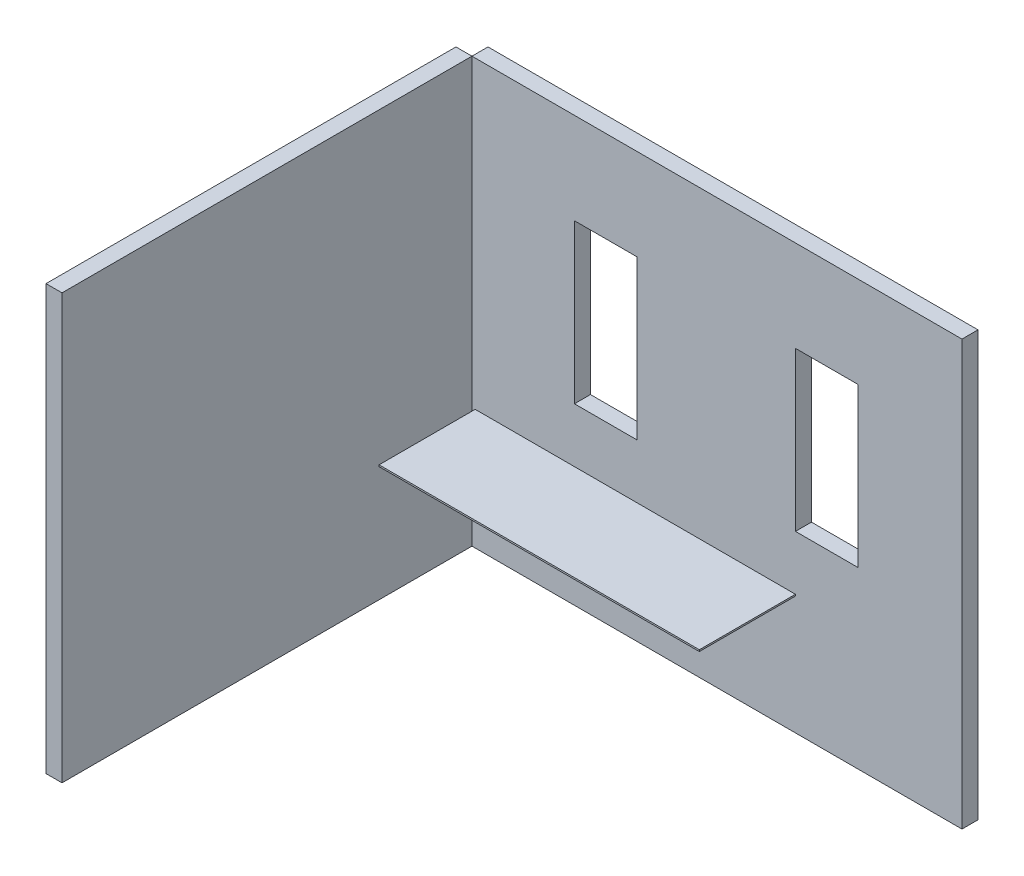
SolidWorks part; units mm, degrees
ref_plane "Plano frontal" through (0, 0, 0) normal (0, 0, 1) x (1, 0, 0)
ref_plane "Plano superior" through (0, 0, 0) normal (0, 1, 0) x (1, 0, 0)
ref_plane "Plano direito" through (0, 0, 0) normal (1, 0, 0) x (0, 0, -1)
sketch "Esboço6" plane through (0, 0, 0) normal (0, 0, 1) x (1, 0, 0)
  line L1 (0, 0) -> (3060, 0)
  line L2 (0, 0) -> (0, 2650)
  line L3 (0, 2650) -> (3060, 2650)
  line L4 (3060, 0) -> (3060, 2650)
extrude "Ressalto-extrusão2" add sketch "Esboço6" along normal blind 100
sketch "Esboço7" plane through (0, 0, 100) normal (0, 0, 1) x (1, 0, 0)
  line L2 (2020, 2080) -> (2020, 1090)
  line L3 (640, 2080) -> (640, 1090)
  line L4 (640, 2080) -> (1030, 2080)
  line L5 (1030, 2080) -> (1030, 1090)
  line L6 (1030, 1090) -> (640, 1090)
  line L7 (2020, 1090) -> (2410, 1090)
  line L8 (2410, 1090) -> (2410, 2080)
  line L9 (2410, 2080) -> (2020, 2080)
extrude "Corte-extrusão1" cut sketch "Esboço7" against normal blind 749
sketch "Esboço8" plane through (0, 0, 100) normal (0, 0, 1) x (1, 0, 0)
  line L1 (0, 2650) -> (-100, 2650)
  line L2 (0, 2650) -> (0, 0)
  line L3 (0, 0) -> (-100, 0)
  line L4 (-100, 2650) -> (-100, 0)
extrude "Ressalto-extrusão3" add sketch "Esboço8" along normal blind 2560 separate body
sketch "Esboço14" plane through (0, 0, 100) normal (0, 0, 1) x (1, 0, 0)
  line L2 (0, 0) -> (3060, 0) construction
  line L3 (20, 740) -> (20, 750)
  line L4 (2020, 740) -> (20, 740)
  line L6 (20, 0) -> (2020, 0)
  line L7 (20, 750) -> (2020, 750)
  line L8 (2020, 750) -> (2020, 740)
extrude "Ressalto-extrusão5" add sketch "Esboço14" along normal blind 600 contours L7 L8 L4 L3
ref_plane "Plano1" through (3060, 2650, 100) normal (0, 1, 0) x (1, 0, 0)
